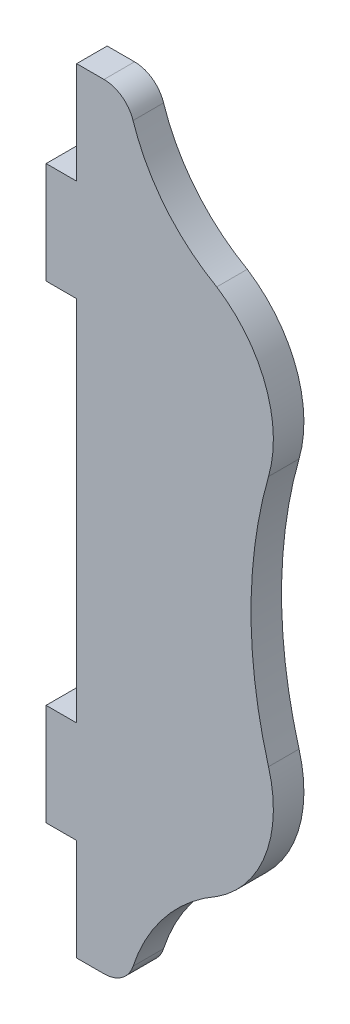
SolidWorks part; units mm, degrees
ref_plane "Alzado" through (0, 0, 0) normal (0, 0, 1) x (1, 0, 0)
ref_plane "Planta" through (0, 0, 0) normal (0, 1, 0) x (1, 0, 0)
ref_plane "Vista lateral" through (0, 0, 0) normal (1, 0, 0) x (0, 0, -1)
sketch "Model" plane through (0, 0, 0) normal (0, 0, 1) x (1, 0, 0)
  line L0 (25.4887, 56.4241) -> (28.1788, 56.4241)
  line L1 (25.4887, -19.6684) -> (28.1788, -19.6684)
  line L2 (25.4887, -9.6684) -> (25.4887, -19.6684)
  line L3 (22.4887, -9.6684) -> (25.4887, -9.6684)
  line L4 (22.4887, 46.4241) -> (25.4887, 46.4241)
  line L5 (22.4887, 46.4241) -> (22.4887, 36.4241)
  line L6 (22.4887, -9.6684) -> (22.4887, 0.3316)
  line L7 (25.4887, 0.3316) -> (22.4887, 0.3316)
  line L8 (25.4887, 36.4241) -> (22.4887, 36.4241)
  line L9 (25.4887, 0.3316) -> (25.4887, 36.4241)
  line L10 (25.4887, 46.4241) -> (25.4887, 56.4241)
  arc A0 (31.0305, 54.3558) -> (39.2525, 44.3107) centre (48.0854, 59.928) ccw
  arc A1 (39.2525, -7.555) -> (31.0305, -17.6001) centre (48.0854, -23.1723) ccw
  arc A2 (39.2525, -7.555) -> (44.3381, 6.0351) centre (32.6601, 2.6586) ccw
  arc A3 (44.3381, 30.7206) -> (39.2525, 44.3107) centre (32.6601, 34.0971) ccw
  arc A4 (44.3381, 30.7206) -> (44.3381, 6.0351) centre (87.7962, 18.3779) ccw
  arc A5 (31.0305, 54.3558) -> (28.1788, 56.4241) centre (28.1788, 53.4241) ccw
  arc A6 (28.1788, -19.6684) -> (31.0305, -17.6001) centre (28.1788, -16.6684) ccw
extrude "Saliente-Extruir1" add sketch "Model" along normal blind 3
